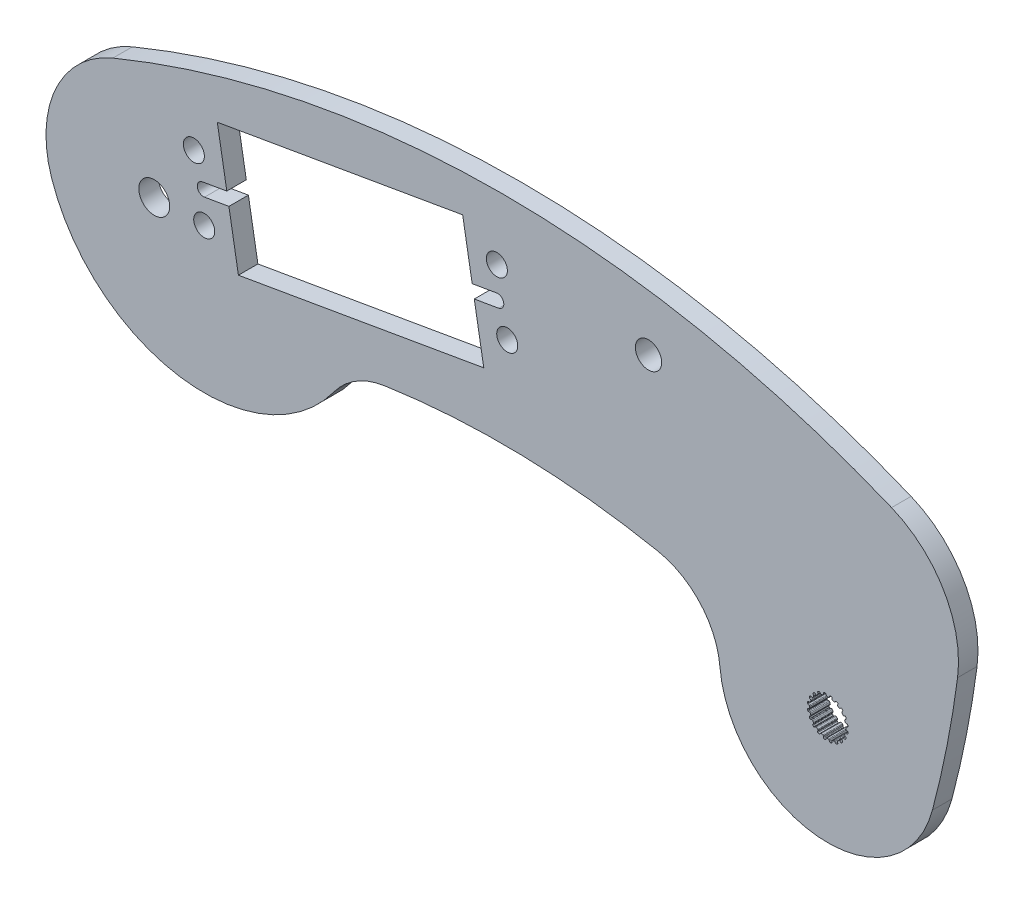
SolidWorks part; units mm, degrees
ref_plane "Front Plane" through (0, 0, 0) normal (0, 0, 1) x (1, 0, 0)
ref_plane "Top Plane" through (0, 0, 0) normal (0, 1, 0) x (1, 0, 0)
ref_plane "Right Plane" through (0, 0, 0) normal (1, 0, 0) x (0, 0, -1)
sketch "Sketch1" plane through (0, 0, 0) normal (0, 0, 1) x (1, 0, 0)
  line L84 (-6.7901, 16.4357) -> (6.7901, -16.4357) construction
  line L85 (121.0901, 16.4357) -> (107.5099, -16.4357) construction
  line L86 (0, 0) -> (114.3, 0) construction
  arc A81 (-6.7901, 16.4357) -> (121.0901, 16.4357) centre (57.15, -138.3341) cw
  arc A82 (6.7901, -16.4357) -> (107.5099, -16.4357) centre (57.15, -138.3341) cw
  arc A84 (-6.7901, 16.4357) -> (6.7901, -16.4357) centre (0, 0) ccw
  arc A85 (121.0901, 16.4357) -> (107.5099, -16.4357) centre (114.3, 0) cw
  dimension "D10" = 131.8914
  dimension "D11" = 35.5662
  dimension "D12" = 114.3
extrude "Boss-Extrude1" add sketch "Sketch1" along normal blind 3.2004
sketch "Sketch2" plane through (0, 0, 3.2004) normal (0, 0, 1) x (1, 0, 0)
  line L0 (30.5042, 19.3666) -> (33.9687, -0.6559) construction
  line L7 (10.3566, 15.8804) -> (50.6518, 22.8528)
  line L13 (22.5307, 7.6759) -> (22.6994, 6.7008) construction
  line L19 (10.3566, 15.8804) -> (13.8211, -4.1421)
  line L20 (13.8211, -4.1421) -> (54.1163, 2.8304)
  line L24 (50.6518, 22.8528) -> (54.1163, 2.8304)
  line L30 (22.6994, 6.7008) -> (15.7284, 5.4946) construction
  line L31 (56.2642, 18.5873) -> (57.9692, 8.7337) construction
  line L32 (6.5037, 9.977) -> (8.2087, 0.1234) construction
  line L33 (57.1167, 13.6605) -> (7.3562, 5.0502) construction
  circle A14 centre (57.9692, 8.7337) radius 1.7272
  circle A15 centre (6.5037, 9.977) radius 1.7272
  circle A16 centre (8.2087, 0.1234) radius 1.7272
  circle A17 centre (56.2642, 18.5873) radius 1.7272
  circle A18 centre (22.5307, 7.6759) radius 3.429 construction
  arc A19 (0, 0) -> (114.3, 0) centre (57.15, -138.3341) cw construction
  arc A20 (107.5099, -16.4357) -> (121.0901, 16.4357) centre (114.3, 0) ccw construction
  arc A21 (-6.7901, 16.4357) -> (6.7901, -16.4357) centre (0, 0) ccw construction
  arc A22 (121.0901, 16.4357) -> (-6.7901, 16.4357) centre (57.15, -138.3341) ccw construction
  circle A23 centre (0, 0) radius 2.54
  point P4 (22.5307, 7.6759)
  point P30 (57.5183, 11.3399)
  point P32 (32.2364, 9.3554)
  dimension "D2" = 5.08
  dimension "D3" = 2.3551
  dimension "D5" = 40.894
  dimension "D10" = 6.858
  dimension "D6" = 23.8023
  dimension "D9" = 3.4544
  dimension "D4" = 20.32
  dimension "D11" = 50.5
  dimension "D12" = 15.4
  dimension "D13" = 10
  dimension "D14" = 7.0746
  dimension "D15" = 0.9896
sketch "Sketch3" plane through (0, 0, 3.2004) normal (0, 0, 1) x (1, 0, 0)
  line L0 (114.3, 0) -> (110.6075, -18.6887) construction
  line L1 (131.9298, -2.3297) -> (96.6702, 2.3297) construction
  line L5 (121.0901, 16.4357) -> (107.5099, -16.4357) construction
  line L6 (0, 0) -> (114.3, 0) construction
  line L7 (93.4164, -14.1385) -> (127.7986, -23.2389) construction
  arc A0 (96.6702, 2.3297) -> (131.9298, -2.3297) centre (114.3, 0) cw
  arc A2 (93.4164, -14.1385) -> (127.7986, -23.2389) centre (110.6075, -18.6887) ccw
  arc A3 (96.6702, 2.3297) -> (93.4164, -14.1385) centre (-34.0845, 19.6087) cw
  arc A4 (131.9298, -2.3297) -> (127.7986, -23.2389) centre (-34.0845, 19.6087) cw
  dimension "D1" = 131.8914
  dimension "D2" = 19.05
  dimension "D3" = 78.823
extrude "Boss-Extrude2" add sketch "Sketch3" against normal up to surface (3.2004 mm away) up to face at (57.15, 2.2751, 0)
extrude "Cut-Extrude1" cut sketch "Sketch2" against normal up to surface (3.2004 mm away) up to face at (78.6299, -5.2945, 0)
sketch "Sketch7" plane through (0, 0, 3.2004) normal (0, 0, 1) x (1, 0, 0)
  line L0 (110.5005, -15.7188) -> (110.7144, -15.7188)
  line L1 (110.9234, -15.4512) -> (110.8612, -15.6312)
  line L2 (110.3111, -15.4521) -> (110.3757, -15.6312)
  line L3 (110.3111, -15.4521) -> (110.9234, -15.4512) construction
  line L4 (110.6075, -15.3635) -> (110.6075, -18.6887) construction
  line L5 (110.3757, -15.6312) -> (110.8612, -15.6312) construction
  line L6 (110.1793, -15.3646) -> (111.0356, -15.3624) construction
  line L7 (111.3258, -15.5189) -> (111.3319, -15.7092)
  line L8 (111.4235, -15.8311) -> (111.6269, -15.8972)
  line L9 (111.9084, -15.7073) -> (111.7936, -15.8592)
  line L10 (112.2701, -15.896) -> (112.2171, -16.0789)
  line L11 (112.2666, -16.2232) -> (112.4397, -16.3489)
  line L12 (112.766, -16.2552) -> (112.6099, -16.3642)
  line L13 (113.0518, -16.5464) -> (112.9448, -16.704)
  line L14 (112.9473, -16.8565) -> (113.073, -17.0296)
  line L15 (113.4124, -17.0413) -> (113.2302, -17.0968)
  line L16 (113.5941, -17.4066) -> (113.4438, -17.5234)
  line L17 (113.3989, -17.6693) -> (113.465, -17.8727)
  line L18 (113.7842, -17.9887) -> (113.5938, -17.9852)
  line L19 (113.8441, -18.3923) -> (113.665, -18.4569)
  line L20 (113.5774, -18.5818) -> (113.5774, -18.7957)
  line L21 (113.845, -19.0046) -> (113.665, -18.9424)
  line L22 (113.7773, -19.407) -> (113.587, -19.4131)
  line L23 (113.465, -19.5047) -> (113.3989, -19.7082)
  line L24 (113.5889, -19.9896) -> (113.437, -19.8749)
  line L25 (113.4002, -20.3514) -> (113.2173, -20.2984)
  line L26 (113.073, -20.3478) -> (112.9473, -20.5209)
  line L27 (113.041, -20.8472) -> (112.9319, -20.6912)
  line L28 (112.7497, -21.133) -> (112.5922, -21.0261)
  line L29 (112.4397, -21.0285) -> (112.2666, -21.1543)
  line L30 (112.2549, -21.4936) -> (112.1994, -21.3115)
  line L31 (111.8896, -21.6753) -> (111.7728, -21.525)
  line L32 (111.6269, -21.4802) -> (111.4235, -21.5463)
  line L33 (111.3075, -21.8654) -> (111.311, -21.675)
  line L34 (110.9039, -21.9254) -> (110.8393, -21.7463)
  line L35 (110.7144, -21.6586) -> (110.5005, -21.6586)
  line L36 (110.2916, -21.9262) -> (110.3537, -21.7463)
  line L37 (109.8892, -21.8585) -> (109.8831, -21.6682)
  line L38 (109.7915, -21.5463) -> (109.588, -21.4802)
  line L39 (109.3066, -21.6702) -> (109.4213, -21.5182)
  line L40 (108.9448, -21.4814) -> (108.9978, -21.2986)
  line L41 (108.9484, -21.1543) -> (108.7753, -21.0285)
  line L42 (108.4489, -21.1222) -> (108.605, -21.0132)
  line L43 (108.1632, -20.831) -> (108.2701, -20.6734)
  line L44 (108.2677, -20.5209) -> (108.1419, -20.3478)
  line L45 (107.8026, -20.3361) -> (107.9847, -20.2806)
  line L46 (107.6208, -19.9708) -> (107.7712, -19.854)
  line L47 (107.816, -19.7082) -> (107.7499, -19.5047)
  line L48 (107.4308, -19.3887) -> (107.6212, -19.3922)
  line L49 (107.3708, -18.9851) -> (107.5499, -18.9205)
  line L50 (107.6376, -18.7957) -> (107.6376, -18.5818)
  line L51 (107.37, -18.3728) -> (107.5499, -18.435)
  line L52 (107.4376, -17.9704) -> (107.628, -17.9643)
  line L53 (107.7499, -17.8727) -> (107.816, -17.6693)
  line L54 (107.626, -17.3878) -> (107.778, -17.5026)
  line L55 (107.8147, -17.0261) -> (107.9976, -17.079)
  line L56 (108.1419, -17.0296) -> (108.2677, -16.8565)
  line L57 (108.1739, -16.5302) -> (108.283, -16.6862)
  line L58 (108.4652, -16.2444) -> (108.6228, -16.3513)
  line L59 (108.7753, -16.3489) -> (108.9484, -16.2232)
  line L60 (108.9601, -15.8838) -> (109.0156, -16.066)
  line L61 (109.3254, -15.7021) -> (109.4422, -15.8524)
  line L62 (109.588, -15.8972) -> (109.7915, -15.8311)
  line L63 (109.9075, -15.512) -> (109.904, -15.7024)
  line L64 (111.0356, -15.3624) -> (111.2275, -15.395)
  line L65 (112.0425, -15.6575) -> (112.215, -15.7478)
  line L66 (112.909, -16.2494) -> (113.0451, -16.3884)
  line L67 (113.5501, -17.08) -> (113.6366, -17.2543)
  line L68 (113.9033, -18.068) -> (113.9316, -18.2606)
  line L69 (113.9337, -19.1169) -> (113.9012, -19.3087)
  line L70 (113.6386, -20.1238) -> (113.5484, -20.2962)
  line L71 (113.0468, -20.9902) -> (112.9077, -21.1263)
  line L72 (112.2162, -21.6314) -> (112.0419, -21.7179)
  line L73 (111.2282, -21.9845) -> (111.0356, -22.0129)
  line L74 (110.1793, -22.015) -> (109.9875, -21.9825)
  line L75 (109.1724, -21.7199) -> (109, -21.6297)
  line L76 (108.306, -21.1281) -> (108.1698, -20.989)
  line L77 (107.6648, -20.2975) -> (107.5783, -20.1231)
  line L78 (107.3117, -19.3094) -> (107.2833, -19.1169)
  line L79 (107.2812, -18.2606) -> (107.3137, -18.0687)
  line L80 (107.5763, -17.2536) -> (107.6665, -17.0812)
  line L81 (108.1681, -16.3872) -> (108.3072, -16.2511)
  line L82 (108.9987, -15.746) -> (109.1731, -15.6596)
  line L83 (109.9868, -15.3929) -> (110.1793, -15.3646)
  circle A0 centre (110.6075, -18.6887) radius 3.429 construction
  arc A1 (93.4164, -14.1385) -> (127.7986, -23.2389) centre (110.6075, -18.6887) ccw construction
  arc A2 (110.8612, -15.6312) -> (110.7144, -15.7188) centre (110.7358, -15.5878) cw
  arc A3 (110.3757, -15.6312) -> (110.5005, -15.7188) centre (110.5005, -15.5861) ccw
  arc A4 (111.2275, -15.395) -> (111.3258, -15.5189) centre (111.1931, -15.5231) cw
  arc A5 (111.3319, -15.7092) -> (111.4235, -15.8311) centre (111.4645, -15.7049) ccw
  arc A6 (110.1793, -15.3646) -> (110.3111, -15.4521) centre (110.1862, -15.4971) cw
  arc A7 (111.0356, -15.3624) -> (110.9234, -15.4512) centre (111.0488, -15.4945) ccw
  arc A8 (111.7936, -15.8592) -> (111.6269, -15.8972) centre (111.6877, -15.7793) cw
  arc A9 (112.0425, -15.6575) -> (111.9084, -15.7073) centre (112.0143, -15.7872) ccw
  arc A10 (112.215, -15.7478) -> (112.2701, -15.896) centre (112.1427, -15.859) cw
  arc A11 (112.2171, -16.0789) -> (112.2666, -16.2232) centre (112.3446, -16.1158) ccw
  arc A12 (112.6099, -16.3642) -> (112.4397, -16.3489) centre (112.5339, -16.2555) cw
  arc A13 (112.909, -16.2494) -> (112.766, -16.2552) centre (112.842, -16.364) ccw
  arc A14 (113.0451, -16.3884) -> (113.0518, -16.5464) centre (112.9419, -16.4719) cw
  arc A15 (112.9448, -16.704) -> (112.9473, -16.8565) centre (113.0547, -16.7785) ccw
  arc A16 (113.2302, -17.0968) -> (113.073, -17.0296) centre (113.1915, -16.9699) cw
  arc A17 (113.5501, -17.08) -> (113.4124, -17.0413) centre (113.4511, -17.1682) ccw
  arc A18 (113.6366, -17.2543) -> (113.5941, -17.4066) centre (113.5127, -17.3018) cw
  arc A19 (113.4438, -17.5234) -> (113.3989, -17.6693) centre (113.5252, -17.6282) ccw
  arc A20 (113.5938, -17.9852) -> (113.465, -17.8727) centre (113.5962, -17.8525) cw
  arc A21 (113.9033, -18.068) -> (113.7842, -17.9887) centre (113.7817, -18.1214) ccw
  arc A22 (113.9316, -18.2606) -> (113.8441, -18.3923) centre (113.7991, -18.2675) cw
  arc A23 (113.665, -18.4569) -> (113.5774, -18.5818) centre (113.7101, -18.5818) ccw
  arc A24 (113.665, -18.9424) -> (113.5774, -18.7957) centre (113.7083, -18.817) cw
  arc A25 (113.9337, -19.1169) -> (113.845, -19.0046) centre (113.8017, -19.13) ccw
  arc A26 (113.9012, -19.3087) -> (113.7773, -19.407) centre (113.7731, -19.2743) cw
  arc A27 (113.587, -19.4131) -> (113.465, -19.5047) centre (113.5913, -19.5457) ccw
  arc A28 (113.437, -19.8749) -> (113.3989, -19.7082) centre (113.5169, -19.7689) cw
  arc A29 (113.6386, -20.1238) -> (113.5889, -19.9896) centre (113.509, -20.0955) ccw
  arc A30 (113.5484, -20.2962) -> (113.4002, -20.3514) centre (113.4372, -20.2239) cw
  arc A31 (113.2173, -20.2984) -> (113.073, -20.3478) centre (113.1804, -20.4258) ccw
  arc A32 (112.9319, -20.6912) -> (112.9473, -20.5209) centre (113.0407, -20.6151) cw
  arc A33 (113.0468, -20.9902) -> (113.041, -20.8472) centre (112.9322, -20.9233) ccw
  arc A34 (112.9077, -21.1263) -> (112.7497, -21.133) centre (112.8243, -21.0232) cw
  arc A35 (112.5922, -21.0261) -> (112.4397, -21.0285) centre (112.5177, -21.1359) ccw
  arc A36 (112.1994, -21.3115) -> (112.2666, -21.1543) centre (112.3263, -21.2728) cw
  arc A37 (112.2162, -21.6314) -> (112.2549, -21.4936) centre (112.1279, -21.5323) ccw
  arc A38 (112.0419, -21.7179) -> (111.8896, -21.6753) centre (111.9944, -21.5939) cw
  arc A39 (111.7728, -21.525) -> (111.6269, -21.4802) centre (111.6679, -21.6064) ccw
  arc A40 (111.311, -21.675) -> (111.4235, -21.5463) centre (111.4437, -21.6775) cw
  arc A41 (111.2282, -21.9845) -> (111.3075, -21.8654) centre (111.1748, -21.863) ccw
  arc A42 (111.0356, -22.0129) -> (110.9039, -21.9254) centre (111.0287, -21.8803) cw
  arc A43 (110.8393, -21.7463) -> (110.7144, -21.6586) centre (110.7144, -21.7913) ccw
  arc A44 (110.3537, -21.7463) -> (110.5005, -21.6586) centre (110.4792, -21.7896) cw
  arc A45 (110.1793, -22.015) -> (110.2916, -21.9262) centre (110.1661, -21.8829) ccw
  arc A46 (109.9875, -21.9825) -> (109.8892, -21.8585) centre (110.0219, -21.8543) cw
  arc A47 (109.8831, -21.6682) -> (109.7915, -21.5463) centre (109.7504, -21.6725) ccw
  arc A48 (109.4213, -21.5182) -> (109.588, -21.4802) centre (109.5272, -21.5982) cw
  arc A49 (109.1724, -21.7199) -> (109.3066, -21.6702) centre (109.2007, -21.5902) ccw
  arc A50 (109, -21.6297) -> (108.9448, -21.4814) centre (109.0723, -21.5184) cw
  arc A51 (108.9978, -21.2986) -> (108.9484, -21.1543) centre (108.8703, -21.2616) ccw
  arc A52 (108.605, -21.0132) -> (108.7753, -21.0285) centre (108.681, -21.122) cw
  arc A53 (108.306, -21.1281) -> (108.4489, -21.1222) centre (108.3729, -21.0135) ccw
  arc A54 (108.1698, -20.989) -> (108.1632, -20.831) centre (108.273, -20.9055) cw
  arc A55 (108.2701, -20.6734) -> (108.2677, -20.5209) centre (108.1603, -20.5989) ccw
  arc A56 (107.9847, -20.2806) -> (108.1419, -20.3478) centre (108.0234, -20.4076) cw
  arc A57 (107.6648, -20.2975) -> (107.8026, -20.3361) centre (107.7639, -20.2092) ccw
  arc A58 (107.5783, -20.1231) -> (107.6208, -19.9708) centre (107.7023, -20.0756) cw
  arc A59 (107.7712, -19.854) -> (107.816, -19.7082) centre (107.6898, -19.7492) ccw
  arc A60 (107.6212, -19.3922) -> (107.7499, -19.5047) centre (107.6187, -19.5249) cw
  arc A61 (107.3117, -19.3094) -> (107.4308, -19.3887) centre (107.4332, -19.256) ccw
  arc A62 (107.2833, -19.1169) -> (107.3708, -18.9851) centre (107.4159, -19.11) cw
  arc A63 (107.5499, -18.9205) -> (107.6376, -18.7957) centre (107.5049, -18.7957) ccw
  arc A64 (107.5499, -18.435) -> (107.6376, -18.5818) centre (107.5066, -18.5604) cw
  arc A65 (107.2812, -18.2606) -> (107.37, -18.3728) centre (107.4133, -18.2474) ccw
  arc A66 (107.3137, -18.0687) -> (107.4376, -17.9704) centre (107.4419, -18.1031) cw
  arc A67 (107.628, -17.9643) -> (107.7499, -17.8727) centre (107.6237, -17.8317) ccw
  arc A68 (107.778, -17.5026) -> (107.816, -17.6693) centre (107.698, -17.6085) cw
  arc A69 (107.5763, -17.2536) -> (107.626, -17.3878) centre (107.706, -17.2819) ccw
  arc A70 (107.6665, -17.0812) -> (107.8147, -17.0261) centre (107.7778, -17.1535) cw
  arc A71 (107.9976, -17.079) -> (108.1419, -17.0296) centre (108.0346, -16.9516) ccw
  arc A72 (108.283, -16.6862) -> (108.2677, -16.8565) centre (108.1742, -16.7623) cw
  arc A73 (108.1681, -16.3872) -> (108.1739, -16.5302) centre (108.2827, -16.4541) ccw
  arc A74 (108.3072, -16.2511) -> (108.4652, -16.2444) centre (108.3907, -16.3543) cw
  arc A75 (108.6228, -16.3513) -> (108.7753, -16.3489) centre (108.6973, -16.2415) ccw
  arc A76 (109.0156, -16.066) -> (108.9484, -16.2232) centre (108.8886, -16.1046) cw
  arc A77 (108.9987, -15.746) -> (108.9601, -15.8838) centre (109.087, -15.8451) ccw
  arc A78 (109.1731, -15.6596) -> (109.3254, -15.7021) centre (109.2206, -15.7835) cw
  arc A79 (109.4422, -15.8524) -> (109.588, -15.8972) centre (109.547, -15.771) ccw
  arc A80 (109.904, -15.7024) -> (109.7915, -15.8311) centre (109.7713, -15.7) cw
  arc A81 (109.9868, -15.3929) -> (109.9075, -15.512) centre (110.0402, -15.5145) ccw
  circle A82 centre (110.6075, -18.6887) radius 12.7 construction
  point P19 (110.6075, -15.7188)
  point P247 (100.0122, -4.2821)
  dimension "D1" = 6.858
  dimension "D4" = 0.1327
  dimension "D9" = 25.4
  dimension "D2" = 0.2139
  dimension "D3" = 0.1904
  dimension "D5" = 0.4855
  dimension "D6" = 0.0877
  dimension "D7" = 0.8563
  dimension "D8" = 2.9699
extrude "Cut-Extrude3" cut sketch "Sketch7" against normal up to surface (3.2004 mm away) up to face at (-2.54, 0, 0)
sketch "Sketch8" plane through (0, 0, 3.2004) normal (0, 0, 1) x (1, 0, 0)
  line L2 (10.3566, 15.8804) -> (13.8211, -4.1421) construction
  line L3 (10.3566, 15.8804) -> (13.8211, -4.1421) construction
  line L4 (7.9111, 6.1773) -> (11.9156, 6.8703)
  line L5 (7.9111, 6.1773) -> (8.2576, 4.1751) construction
  line L6 (54.1163, 2.8304) -> (50.6518, 22.8528) construction
  line L7 (8.2576, 4.1751) -> (12.2621, 4.868)
  line L8 (11.9156, 6.8703) -> (12.2621, 4.868)
  line L9 (52.2108, 13.8427) -> (56.2153, 14.5356)
  line L10 (52.2108, 13.8427) -> (52.5573, 11.8405)
  line L11 (52.5573, 11.8405) -> (56.5618, 12.5334)
  line L12 (56.2153, 14.5356) -> (56.5618, 12.5334) construction
  arc A6 (56.2153, 14.5356) -> (56.5618, 12.5334) centre (56.3885, 13.5345) cw
  arc A7 (7.9111, 6.1773) -> (8.2576, 4.1751) centre (8.0844, 5.1762) ccw
  point P22 (12.0888, 5.8691)
  point P23 (52.3841, 12.8416)
  dimension "D4" = 4.064
  dimension "D5" = 2.032
extrude "Cut-Extrude4" cut sketch "Sketch8" against normal up to surface (3.2004 mm away) up to face at (78.6299, -5.2945, 0)
fillet "Fillet1" radius 12.7 1 edges at (94.0356, -11.7056, 1.6002)
sketch "Sketch9" plane through (0, 0, 0) normal (0, 0, -1) x (-1, 0, 0)
  line L0 (-37.8089, -7.8686) -> (16.8684, -5.63)
  line L2 (0, 0) -> (-114.3, 0) construction
  arc A0 (-37.8089, -7.8686) -> (-29.5382, -12.8633) centre (-39.6449, -20.2538) cw
  arc A1 (-29.5382, -12.8633) -> (16.8684, -5.63) centre (-8.2029, 2.7378) ccw
  arc A4 (-6.7901, -16.4357) -> (-82.7062, -8.9424) centre (-57.15, -138.3341) ccw construction
  arc A5 (-6.7901, -16.4357) -> (6.7901, 16.4357) centre (0, 0) ccw construction
  dimension "D1" = 54.723
  dimension "D2" = 9.6619
  dimension "D3" = 7.8686
extrude "Boss-Extrude3" add sketch "Sketch9" against normal up to surface (3.2004 mm away) up to face at (2.54, 0, 3.2004)
sketch "Sketch10" plane through (0, 0, 0) normal (0, 0, -1) x (-1, 0, 0)
  line L0 (-81.1715, 18.1918) -> (-81.1715, 0) construction
  line L2 (0, 0) -> (-114.3, 0) construction
  circle A0 centre (-81.1715, 18.1918) radius 2.159
  dimension "D1" = 4.318
  dimension "D2" = 18.1918
  dimension "D3" = 33.1285
extrude "Cut-Extrude5" cut sketch "Sketch10" against normal up to surface (3.2004 mm away) up to face at (2.54, 0, 3.2004)
